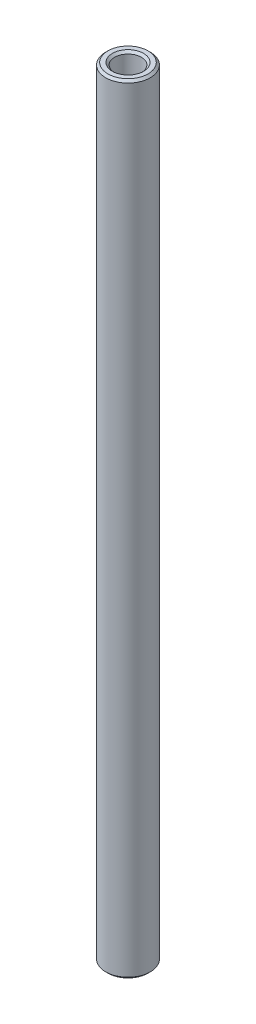
SolidWorks part; units mm, degrees
ref_plane "Front Plane" through (0, 0, 0) normal (0, 0, 1) x (1, 0, 0)
ref_plane "Top Plane" through (0, 0, 0) normal (0, 1, 0) x (1, 0, 0)
ref_plane "Right Plane" through (0, 0, 0) normal (1, 0, 0) x (0, 0, -1)
sketch "Sketch1" plane through (0, 0, 0) normal (0, 1, 0) x (1, 0, 0)
  circle A0 centre (0, 0) radius 10
extrude "Boss-Extrude1" add sketch "Sketch1" along normal blind 175
chamfer "Chamfer2" distance 0.5 angle 45 2 edges at (0, 175, 10) (0, 0, 10)
sketch "Sketch2" plane through (0, 175, 0) normal (0, 1, 0) x (1, 0, 0)
  circle A0 centre (0, 0) radius 3
extrude "Cut-Extrude1" cut sketch "Sketch2" against normal blind 20
chamfer "Chamfer3" distance 0.5 angle 45 1 edges at (0, 175, 3)
sketch "Sketch3" plane through (0, 0, 0) normal (0, -1, 0) x (1, 0, 0)
  circle A0 centre (0, 0) radius 3
extrude "Cut-Extrude2" cut sketch "Sketch3" against normal blind 20
sketch "Sketch4" plane through (0, 0, 0) normal (0, -1, 0) x (1, 0, 0)
  circle A0 centre (0, 0) radius 5
  circle A1 centre (0, 0) radius 10
extrude "Cut-Extrude3" cut sketch "Sketch4" against normal blind 273
chamfer "Chamfer5" distance 0.5 angle 45 3 edges at (0, 175, 5) (0, 0, -3) (0, 0, -5)
